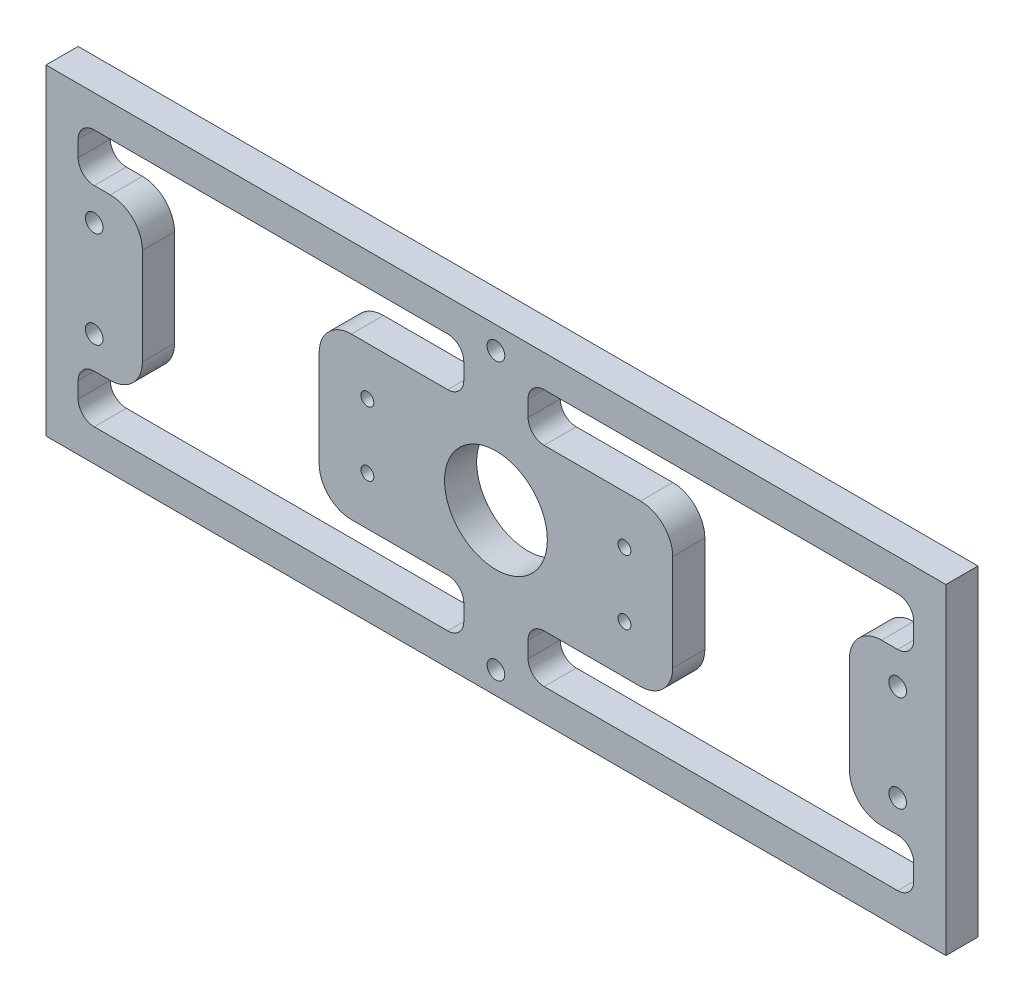
SolidWorks part; units mm, degrees
material "1060 Alloy"
ref_plane "Front Plane" through (0, 0, 0) normal (0, 0, 1) x (1, 0, 0)
ref_plane "Top Plane" through (0, 0, 0) normal (0, 1, 0) x (1, 0, 0)
ref_plane "Right Plane" through (0, 0, 0) normal (1, 0, 0) x (0, 0, -1)
sketch "Sketch1" plane through (0, 0, 0) normal (0, 0, 1) x (1, 0, 0)
  line L0 (0, 50) -> (280, 50) construction
  line L1 (0, 0) -> (280, 0)
  line L2 (0, 0) -> (0, 100)
  line L3 (0, 100) -> (280, 100)
  line L4 (280, 0) -> (280, 100)
  line L5 (140, 0) -> (140, 100) construction
  circle A0 centre (180, 60) radius 2
  circle A1 centre (180, 40) radius 2
  circle A2 centre (100, 60) radius 2
  circle A3 centre (100, 40) radius 2
  circle A4 centre (140, 50) radius 16
  dimension "D5" = 4
  dimension "D6" = 32
  dimension "D1" = 280
  dimension "D2" = 100
  dimension "D3" = 40
  dimension "D4" = 10
extrude "Boss-Extrude1" add sketch "Sketch1" along normal blind 10
sketch "Sketch2" plane through (0, 0, 0) normal (0, 0, -1) x (-1, 0, 0)
  line L0 (0, 50) -> (-280, 50) construction
  line L1 (0, 100) -> (0, 0) construction
  line L2 (-280, 0) -> (-280, 100) construction
  line L3 (-140, 50) -> (-140, 100) construction
  line L4 (-280, 100) -> (0, 100) construction
  circle A0 centre (-15, 35) radius 2.75
  circle A1 centre (-15, 65) radius 2.75
  circle A2 centre (-265, 35) radius 2.75
  circle A3 centre (-265, 65) radius 2.75
  dimension "D2" = 5.5
  dimension "D1" = 125
  dimension "D3" = 15
extrude "Cut-Extrude1" cut sketch "Sketch2" against normal through all
sketch "Sketch3" plane through (0, 0, 0) normal (0, 0, -1) x (-1, 0, 0)
  circle A0 centre (-265, 65) radius 4.5
  circle A1 centre (-265, 35) radius 4.5
  circle A2 centre (-15, 35) radius 4.5
  circle A3 centre (-15, 65) radius 4.5
  dimension "D1" = 9
extrude "Cut-Extrude2" cut sketch "Sketch3" against normal blind 5
sketch "Sketch4" plane through (0, 0, 10) normal (0, 0, 1) x (1, 0, 0)
  line L0 (140, 0) -> (140, 100) construction
  line L1 (0, 0) -> (280, 0) construction
  line L2 (280, 100) -> (0, 100) construction
  line L3 (0, 50) -> (280, 50) construction
  line L4 (0, 100) -> (0, 0) construction
  line L5 (280, 0) -> (280, 100) construction
  line L6 (10, 25) -> (30, 25)
  line L7 (10, 75) -> (30, 75)
  line L8 (30, 25) -> (30, 75)
  line L9 (10, 25) -> (10, 10)
  line L10 (10, 10) -> (130, 10)
  line L11 (130, 10) -> (130, 25)
  line L12 (130, 25) -> (85, 25)
  line L13 (130, 75) -> (85, 75)
  line L14 (85, 25) -> (85, 75)
  line L15 (130, 90) -> (130, 75)
  line L16 (10, 90) -> (130, 90)
  line L17 (10, 75) -> (10, 90)
  line L18 (150, 90) -> (150, 75)
  line L19 (150, 10) -> (150, 25)
  line L20 (150, 25) -> (195, 25)
  line L21 (195, 25) -> (195, 75)
  line L22 (150, 75) -> (195, 75)
  line L23 (270, 90) -> (150, 90)
  line L24 (270, 75) -> (270, 90)
  line L25 (270, 75) -> (250, 75)
  line L26 (250, 25) -> (250, 75)
  line L27 (270, 25) -> (250, 25)
  line L28 (270, 25) -> (270, 10)
  line L29 (270, 10) -> (150, 10)
  point P23 (85, 50)
  point P26 (30, 50)
  dimension "D1" = 10
  dimension "D2" = 10
  dimension "D3" = 10
  dimension "D4" = 30
  dimension "D5" = 55
  dimension "D6" = 15
extrude "Cut-Extrude3" cut sketch "Sketch4" against normal through all
fillet "Fillet1" radius 10 8 edges at (85, 75, 5) (250, 75, 5) (195, 75, 5) (250, 25, 5) (195, 25, 5) (85, 25, 5) (30, 25, 5) (30, 75, 5)
fillet "Fillet2" radius 5 16 edges at (150, 75, 5) (150, 10, 5) (10, 10, 5) (130, 10, 5) (270, 75, 5) (270, 10, 5) (130, 75, 5) (270, 25, 5) (270, 90, 5) (130, 90, 5) (130, 25, 5) (10, 25, 5) (150, 25, 5) (150, 90, 5) (10, 90, 5) (10, 75, 5)
sketch "Sketch5" plane through (0, 0, 10) normal (0, 0, 1) x (1, 0, 0)
  line L0 (140, 100) -> (140, 0) construction
  line L1 (280, 100) -> (0, 100) construction
  line L2 (0, 0) -> (280, 0) construction
  line L3 (0, 50) -> (280, 50) construction
  line L4 (0, 100) -> (0, 0) construction
  line L5 (280, 0) -> (280, 100) construction
  circle A0 centre (140, 7) radius 2.75
  circle A1 centre (140, 93) radius 2.75
  dimension "D1" = 5.5
  dimension "D2" = 7
extrude "Cut-Extrude4" cut sketch "Sketch5" against normal through all
sketch "Sketch6" plane through (0, 0, 0) normal (0, 0, -1) x (-1, 0, 0)
  circle A0 centre (-140, 7) radius 4.5
  circle A1 centre (-140, 93) radius 4.5
  dimension "D1" = 9
extrude "Cut-Extrude5" cut sketch "Sketch6" against normal blind 5
